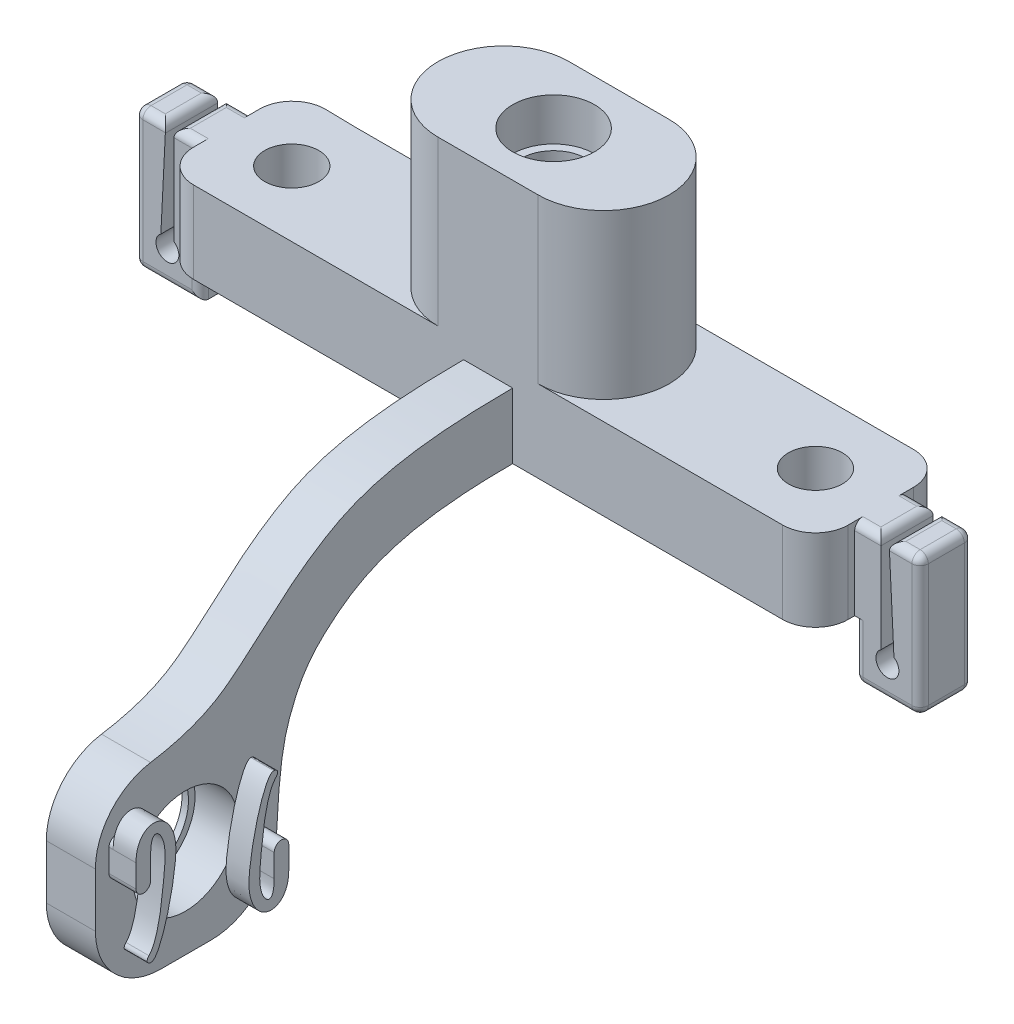
SolidWorks part; units mm, degrees
ref_plane "Front Plane" through (0, 0, 0) normal (0, 0, 1) x (1, 0, 0)
ref_plane "Top Plane" through (0, 0, 0) normal (0, 1, 0) x (1, 0, 0)
ref_plane "Right Plane" through (0, 0, 0) normal (1, 0, 0) x (0, 0, -1)
sketch "Sketch1" plane through (0, 0, 0) normal (0, 1, 0) x (1, 0, 0)
  line L0 (-29.8679, 0) -> (88.5042, 0) construction
  line L1 (0, 8.6524) -> (0, -33.8157) construction
  line L2 (16, -4) -> (20, -4)
  line L3 (20, -4) -> (20, 4)
  line L4 (20, 4) -> (16, 4)
  line L5 (-16, -4) -> (-20, -4)
  line L6 (-20, -4) -> (-20, 4.069)
  line L7 (-20, 4.069) -> (-16, 4)
  circle A0 centre (-16, 0) radius 1.65
  circle A1 centre (16, 0) radius 1.65
  arc A2 (-16, 4) -> (-16, -4) centre (-16, 0) ccw construction
  arc A3 (16, -4) -> (16, 4) centre (16, 0) ccw construction
  spline S0 degree 3 poles (16, -4) (10.304, -4) (-0.6321, -4) (-9.0398, -4) (-16, -4) knots 0 0 0 0 0.5 1 1 1 1
  spline S1 degree 3 poles (16, 4) (9.0398, 4) (0.6321, 4) (-10.304, 4) (-16, 4) knots 0 0 0 0 0.5 1 1 1 1
  point P15 (0, 13)
  point P16 (0, -13)
  point P17 (0, -4)
  point P18 (0, 4)
  dimension "D3" = 3.3
  dimension "D4" = 3.3
  dimension "D5" = 4
  dimension "D6" = 4
  dimension "D7" = 4
  dimension "D1" = 16
  dimension "D2" = 16
  dimension "D8" = 4
extrude "Boss-Extrude1" add sketch "Sketch1" along normal blind 5
sketch "Sketch5" plane through (0, 5, 0) normal (0, 1, 0) x (1, 0, 0)
  circle A0 centre (-4, 2.5) radius 0.75
  circle A1 centre (4, -2.5) radius 0.75
  point P0 (-4, 2.5)
  dimension "D1" = 1.5
  dimension "D6" = 1.5
  dimension "D2" = 4
  dimension "D3" = 2.5
  dimension "D4" = 4
  dimension "D5" = 2.5
sketch "Sketch6" plane through (0, 0, 0) normal (0, -1, 0) x (1, 0, 0)
  circle A0 centre (0, 0) radius 2.5
  dimension "D1" = 5
extrude "Cut-Extrude1" cut sketch "Sketch6" against normal blind 2.6
sketch "Sketch7" plane through (0, 5, 0) normal (0, 1, 0) x (1, 0, 0)
  line L0 (3.0587, 0) -> (-3.0587, 0) construction
  line L4 (-29.8679, 0) -> (88.5042, 0) construction
  line L5 (3.0587, -4) -> (-3.0587, -4)
  line L6 (3.0587, 4) -> (-3.0587, 4)
  arc A2 (3.0587, -4) -> (3.0587, 4) centre (3.0587, 0) ccw
  arc A3 (-3.0587, 4) -> (-3.0587, -4) centre (-3.0587, 0) ccw
  spline S0 degree 3 poles (16, 4) (9.0398, 4) (0.6321, 4) (-10.304, 4) (-16, 4) knots 0 0 0 0 0.5 1 1 1 1 construction
  point P5 (0, 0)
extrude "Boss-Extrude2" add sketch "Sketch7" along normal blind 10
sketch "Sketch8" plane through (0, 15, 0) normal (0, 1, 0) x (1, 0, 0)
  circle A0 centre (0, 0) radius 2.5
  dimension "D1" = 5
extrude "Cut-Extrude2" cut sketch "Sketch8" against normal blind 2.6
sketch "Sketch9" plane through (0, 15, 0) normal (0, 1, 0) x (1, 0, 0)
  circle A0 centre (0, 0) radius 2
  dimension "D1" = 4
extrude "Cut-Extrude3" cut sketch "Sketch9" against normal through all both and the other way through all
sketch "Sketch10" plane through (0, 0, 0) normal (0, 0, 1) x (1, 0, 0)
  line L0 (20, 5) -> (24, 5)
  line L1 (24, 5) -> (24, -3.5)
  line L2 (24, -3.5) -> (20, -3.5)
  line L3 (20, -3.5) -> (20, 0)
  line L4 (20, 0) -> (20, 5)
  line L5 (0, 0) -> (0, 15) construction
  line L6 (-3.0587, 15) -> (3.0587, 15) construction
  line L7 (-20, -3.5) -> (-20, 0)
  line L8 (-24, -3.5) -> (-20, -3.5)
  line L9 (-24, 5) -> (-24, -3.5)
  line L10 (-20, 5) -> (-24, 5)
  line L11 (-20, 0) -> (-20, 5)
  line L13 (-16, 0) -> (16, 0) construction
  dimension "D1" = 3.5
  dimension "D2" = 4
extrude "Boss-Extrude3" add sketch "Sketch10" along normal blind 1.6 and the other way blind 1.6
sketch "Sketch11" plane through (0, 0, 0) normal (0, 0, 1) x (1, 0, 0)
  line L1 (0, 0) -> (0, 15) construction
  line L4 (21.6, 5) -> (21.6, -1)
  line L5 (-3.0587, 15) -> (3.0587, 15) construction
  line L6 (24, 5) -> (20, 5) construction
  line L7 (21.6, 5) -> (22.1, 5)
  line L8 (22.1, 5) -> (22.4, -1)
  line L9 (21.6, -1) -> (22.4, -1) construction
  line L11 (-22.1, 5) -> (-22.4, -1)
  line L12 (-21.6, 5) -> (-21.6, -1)
  line L13 (-21.6, 5) -> (-22.1, 5)
  line L14 (22, -3.5) -> (22, 5) construction
  line L15 (20, -3.5) -> (24, -3.5) construction
  arc A0 (21.6, -1) -> (22.4, -1) centre (22, -1.5745) ccw
  arc A1 (-21.6, -1) -> (-22.4, -1) centre (-22, -1.5745) cw
  dimension "D5" = 6
  dimension "D4" = 0.7
  dimension "D2" = 0.5
  dimension "D3" = 0.8
extrude "Cut-Extrude4" cut sketch "Sketch11" against normal up to surface and the other way up to surface up to face at (-21.6, 0.6, -1.6) other way up to face at (-21.6, 0.6, 1.6)
fillet "Fillet1" radius 0.5 29 edges at (24, -3.5, 0) (-21.6, 5, 0) (-22.1, 5, 0) (22.1, 5, 0) (21.6, 5, 0) (20.8, 5, 1.6) (20.8, 5, -1.6) (24, 0.75, -1.6) (22, -3.5, -1.6) (-20.8, 5, -1.6) (-23.05, 5, -1.6) (-20, -1.75, -1.6) (-22, -3.5, -1.6) (-20, -1.75, 1.6) (20, -3.5, 0) (20, -1.75, -1.6) (23.05, 5, -1.6) (24, 5, 0) (23.05, 5, 1.6) (24, 0.75, 1.6) (22, -3.5, 1.6) (20, -1.75, 1.6) (-24, 0.75, -1.6) (-24, -3.5, 0) (-22, -3.5, 1.6) (-24, 0.75, 1.6) (-24, 5, 0) (-20.8, 5, 1.6) (-23.05, 5, 1.6)
fillet "Fillet2" radius 2 4 edges at (-20, 2.5, -4.069) (-20, 2.5, 4) (20, 2.5, -4) (20, 2.5, 4)
sketch "Sketch14" plane through (0, 0, 0) normal (1, 0, 0) x (0, 0, -1)
  line L0 (-4, 0) -> (-4, 4)
  line L1 (-4, 0) -> (-4, 5) construction
  line L2 (-29.5, -10.5) -> (-18.5, -10.5) construction
  line L4 (-29.5, -5) -> (-29.5, -16)
  line L5 (-29.5, -16) -> (-18.5, -16)
  line L7 (-24, -5) -> (-24, -16) construction
  circle A0 centre (-24, -10.5) radius 3.19
  spline S0 degree 3 poles (-29.5, -5) (-26.4104, -5) (-22.9486, -4.2502) (-18.0193, -0.1689) (-18.0651, 0.0337) (-14.0665, 2.8073) (-10.8115, 4) (-4, 4) knots 0 0 0 0 0.14442 0.201418 0.529032 0.612985 1 1 1 1
  spline S1 degree 3 poles (-18.5, -16) (-18.5, -13.9242) (-18.4126, -9.0031) (-17.1856, -5.2248) (-16.289, -3.8909) (-12.9293, -1.0537) (-9.8052, 0) (-4, 0) knots 0 0 0 0 0.247521 0.303911 0.535012 0.607509 1 1 1 1
  point P13 (-24, -10.5)
  dimension "D4" = 6.38
  dimension "D7" = 11
  dimension "D1" = 4
  dimension "D3" = 11
  dimension "D5" = 24
  dimension "D6" = 10.5
extrude "Boss-Extrude5" add sketch "Sketch14" along normal blind 1.5 and the other way blind 1.5
fillet "Fillet3" radius 4 3 edges at (0, -16, 18.5) (0, -16, 29.5) (0, -5, 29.5)
sketch "Sketch15" plane through (1.5, 0, 0) normal (1, 0, 0) x (0, 0, -1)
  line L0 (-28.2204, -9.3567) -> (-28.2204, -7.9677) construction
  line L1 (-28.6662, -9.3567) -> (-28.6662, -7.9677) construction
  line L2 (-27.7745, -9.3567) -> (-27.7745, -7.9677) construction
  line L3 (-28.6662, -7.9677) -> (-28.6662, -9.3567)
  line L4 (-27.7745, -7.9677) -> (-27.7745, -9.3567)
  line L5 (-24, -10.5) -> (-24, -7.31) construction
  line L6 (-24, -10.5) -> (-27.19, -10.5) construction
  line L7 (-19.7796, -11.6433) -> (-19.7796, -13.0323) construction
  line L8 (-19.3338, -11.6433) -> (-19.3338, -13.0323) construction
  line L9 (-20.2255, -11.6433) -> (-20.2255, -13.0323) construction
  line L10 (-19.3338, -13.0323) -> (-19.3338, -11.6433)
  line L11 (-20.2255, -13.0323) -> (-20.2255, -11.6433)
  arc A0 (-28.6662, -9.3567) -> (-27.7745, -9.3567) centre (-28.2204, -9.3567) ccw construction
  arc A1 (-27.7745, -7.9677) -> (-28.6662, -7.9677) centre (-28.2204, -7.9677) ccw construction
  arc A2 (-28.6662, -9.3567) -> (-27.7745, -9.3567) centre (-28.2204, -9.3567) ccw
  arc A3 (-19.3338, -11.6433) -> (-20.2255, -11.6433) centre (-19.7796, -11.6433) ccw construction
  arc A4 (-20.2255, -13.0323) -> (-19.3338, -13.0323) centre (-19.7796, -13.0323) ccw construction
  arc A5 (-19.3338, -11.6433) -> (-20.2255, -11.6433) centre (-19.7796, -11.6433) ccw
  spline S0 degree 3 poles (-28.6662, -7.9677) (-28.6662, -6.8459) (-27.3639, -5.8289) (-26.1449, -7.3682) (-26.3584, -10.6965) (-27.2573, -13.7881) (-27.7641, -13.6903) knots 0 0 0 0 0.217284 0.494282 0.572553 1 1 1 1
  spline S1 degree 3 poles (-27.7745, -7.9677) (-27.7745, -7.4866) (-27.5872, -6.6324) (-26.7875, -7.5299) (-27.0704, -10.8759) (-27.3383, -12.6963) (-27.8786, -13.2752) knots 0 0 0 0 0.169551 0.459413 0.542458 1 1 1 1
  spline S2 degree 3 poles (-27.8786, -13.2752) (-27.9805, -13.3843) (-28.0344, -13.5423) (-27.8241, -13.7158) (-27.792, -13.6849) (-27.7641, -13.6903) knots 0 0 0 0 0.41622 0.51622 1 1 1 1
  spline S3 degree 3 poles (-19.3338, -13.0323) (-19.3338, -14.1541) (-20.6361, -15.1711) (-21.8551, -13.6318) (-21.6416, -10.3035) (-20.7427, -7.2119) (-20.2359, -7.3097) knots 0 0 0 0 0.217284 0.494282 0.572553 1 1 1 1
  spline S4 degree 3 poles (-20.2255, -13.0323) (-20.2255, -13.5134) (-20.4128, -14.3676) (-21.2125, -13.4701) (-20.9296, -10.1241) (-20.6617, -8.3037) (-20.1214, -7.7248) knots 0 0 0 0 0.169551 0.459413 0.542458 1 1 1 1
  spline S5 degree 3 poles (-20.1214, -7.7248) (-20.0195, -7.6157) (-19.9656, -7.4577) (-20.1759, -7.2842) (-20.208, -7.3151) (-20.2359, -7.3097) knots 0 0 0 0 0.41622 0.51622 1 1 1 1
  point P2 (-28.2204, -8.6622)
  point P24 (-19.7796, -12.3378)
  point P41 (-24, -10.5)
extrude "Boss-Extrude6" add sketch "Sketch15" along normal blind 1.4 from offset 0.25 separate body
sketch "Sketch16" plane through (1.75, 0, 0) normal (-1, 0, 0) x (0, 0, 1)
  line L0 (19.7796, -13.0323) -> (19.7796, -11.6433) construction
  line L1 (19.3338, -13.0323) -> (19.3338, -11.6433)
  line L2 (20.2255, -13.0323) -> (20.2255, -11.6433)
  line L3 (28.2204, -9.3567) -> (28.2204, -7.9677) construction
  line L4 (27.7745, -9.3567) -> (27.7745, -7.9677)
  line L5 (28.6662, -9.3567) -> (28.6662, -7.9677)
  line L6 (20.2255, -13.0323) -> (20.2255, -11.6433) construction
  line L7 (28.6662, -7.9677) -> (28.6662, -9.3567) construction
  arc A0 (19.3338, -13.0323) -> (20.2255, -13.0323) centre (19.7796, -13.0323) ccw
  arc A1 (20.2255, -11.6433) -> (19.3338, -11.6433) centre (19.7796, -11.6433) ccw
  arc A2 (27.7745, -9.3567) -> (28.6662, -9.3567) centre (28.2204, -9.3567) ccw
  arc A3 (28.6662, -7.9677) -> (27.7745, -7.9677) centre (28.2204, -7.9677) ccw
  point P4 (19.7796, -12.3378)
  point P9 (28.2204, -8.6622)
extrude "Boss-Extrude7" add sketch "Sketch16" along normal up to surface (0.25 mm away) up to face at (1.5, -8.5455, 19.5495)
sketch "Sketch17" plane through (-1.5, 0, 0) normal (-1, 0, 0) x (0, 0, 1)
  circle A0 centre (24, -10.5) radius 3.19
  circle A1 centre (24, -10.5) radius 2.79
  circle A2 centre (24, -10.5) radius 3.19 construction
  dimension "D1" = 0.4
extrude "Boss-Extrude8" add sketch "Sketch17" against normal blind 0.4
